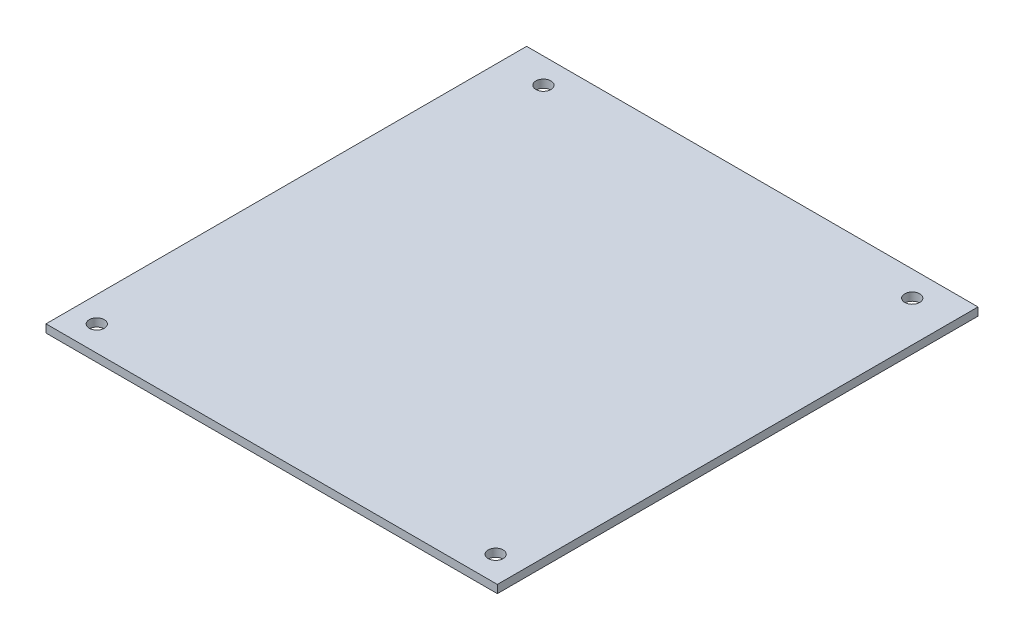
SolidWorks part; units mm, degrees
material "Custom Plastic"
ref_plane "Front Plane" through (0, 0, 0) normal (0, 0, 1) x (1, 0, 0)
ref_plane "Top Plane" through (0, 0, 0) normal (0, 1, 0) x (1, 0, 0)
ref_plane "Right Plane" through (0, 0, 0) normal (1, 0, 0) x (0, 0, -1)
sketch "Sketch2" plane through (0, 0, 0) normal (0, 1, 0) x (1, 0, 0)
  line L1 (0, 0) -> (84.57, 0)
  line L2 (0, 0) -> (0, 90.8)
  line L3 (0, 90.8) -> (84.57, 90.8)
  line L4 (84.57, 0) -> (84.57, 90.8)
extrude "Boss-Extrude1" add sketch "Sketch2" along normal blind 1.6
sketch "Sketch3" plane through (0, 1.6, 0) normal (0, 1, 0) x (1, 0, 0)
  line L3 (0, 0) -> (84.57, 0) construction
  line L4 (84.57, 90.8) -> (0, 90.8) construction
  circle A0 centre (2.5, 2.5) radius 1.5
  circle A1 centre (82.07, 2.5) radius 1.5
  circle A2 centre (5.8, 88.3) radius 1.5
  circle A3 centre (79.37, 88.3) radius 1.5
extrude "Cut-Extrude1" cut sketch "Sketch3" against normal through all
sketch "Sketch4" plane through (84.57, 0, 0) normal (1, 0, 0) x (0, 0, -1)
  line L1 (90.8, 1.6) -> (0, 1.6)
  line L2 (90.8, 1.6) -> (90.8, 0)
  line L3 (90.8, 0) -> (0, 0)
  line L4 (0, 1.6) -> (0, 0)
extrude "Boss-Extrude2" add sketch "Sketch4" along normal blind 2.88
sketch "Sketch5" plane through (0, 0, 0) normal (-1, 0, 0) x (0, 0, 1)
  line L1 (-90.8, 0) -> (0, 0)
  line L2 (-90.8, 0) -> (-90.8, 1.6)
  line L3 (-90.8, 1.6) -> (0, 1.6)
  line L4 (0, 0) -> (0, 1.6)
extrude "Boss-Extrude3" add sketch "Sketch5" along normal blind 2.59
sketch "Sketch6" plane through (0, 0, -90.8) normal (0, 0, -1) x (-1, 0, 0)
  line L1 (2.59, 0) -> (-87.45, 0)
  line L2 (2.59, 0) -> (2.59, 1.6)
  line L3 (2.59, 1.6) -> (-87.45, 1.6)
  line L4 (-87.45, 0) -> (-87.45, 1.6)
extrude "Boss-Extrude4" add sketch "Sketch6" along normal blind 2.54
sketch "Sketch7" plane through (0, 0, 0) normal (0, 0, 1) x (1, 0, 0)
  line L1 (87.45, 1.6) -> (-2.59, 1.6)
  line L2 (87.45, 1.6) -> (87.45, 0)
  line L3 (87.45, 0) -> (-2.59, 0)
  line L4 (-2.59, 1.6) -> (-2.59, 0)
extrude "Boss-Extrude5" add sketch "Sketch7" along normal blind 2.54
sketch "Sketch8" plane through (0, 0, 0) normal (0, -1, 0) x (1, 0, 0)
  line L0 (-2.59, -93.34) -> (-2.59, 2.54) construction
  line L1 (-2.59, 2.54) -> (87.45, 2.54) construction
  circle A0 centre (42.43, -45.4) radius 2
  point P4 (42.43, 2.54)
  dimension "D1" = 45.02
  dimension "D2" = 47.94
extrude "Boss-Extrude6" [suppressed] add sketch "Sketch8" along normal blind 6
